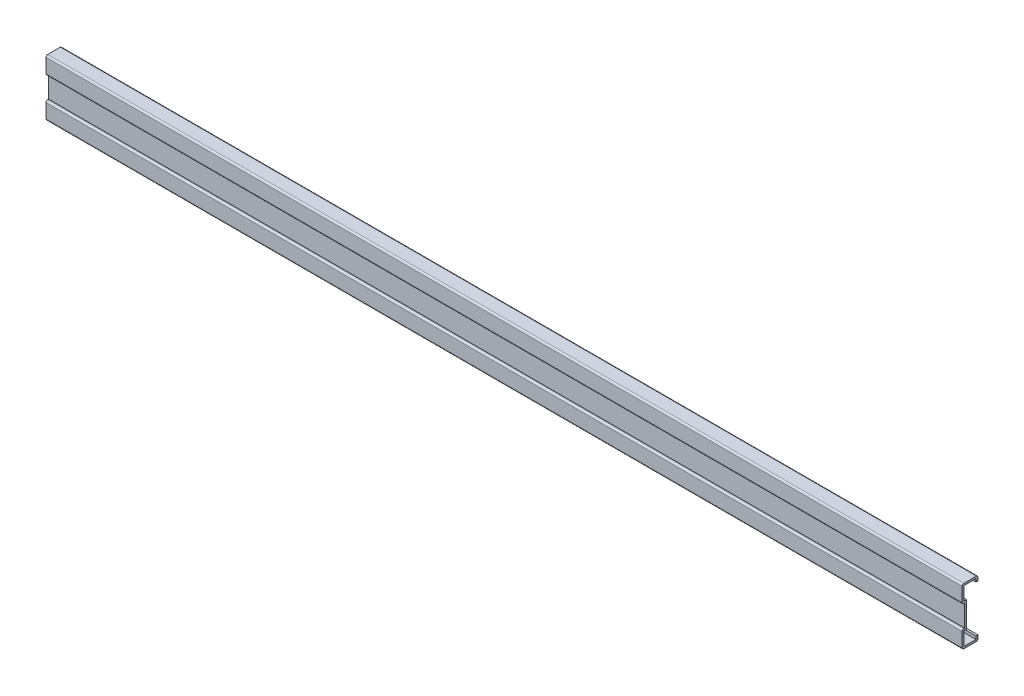
SolidWorks part; units mm, degrees
ref_plane "Спереди" through (0, 0, 0) normal (0, 0, 1) x (1, 0, 0)
ref_plane "Сверху" through (0, 0, 0) normal (0, 1, 0) x (1, 0, 0)
ref_plane "Справа" through (0, 0, 0) normal (1, 0, 0) x (0, 0, -1)
sketch "Эскиз1" plane through (0, 0, 0) normal (1, 0, 0) x (0, 0, -1)
  line L0 (0, 6.5) -> (0, -6.5)
  line L1 (-12.4481, 0) -> (26.4522, 0) construction
  line L2 (0, -6.5) -> (-0.5, -6.5)
  line L3 (-1.5, -7.5) -> (-1.5, -16)
  line L4 (-0.5, -17) -> (7, -17)
  line L5 (8, -16) -> (8, -14)
  line L6 (8, 16) -> (8, 14)
  line L7 (-0.5, 17) -> (7, 17)
  line L8 (-1.5, 7.5) -> (-1.5, 16)
  line L9 (0, 6.5) -> (-0.5, 6.5)
  arc A0 (7, -17) -> (8, -16) centre (7, -16) ccw
  arc A1 (-1.5, -7.5) -> (-0.5, -6.5) centre (-0.5, -7.5) cw
  arc A2 (-1.5, 16) -> (-0.5, 17) centre (-0.5, 16) cw
  arc A3 (-1.5, -16) -> (-0.5, -17) centre (-0.5, -16) ccw
  arc A4 (-1.5, 7.5) -> (-0.5, 6.5) centre (-0.5, 7.5) ccw
  arc A5 (7, 17) -> (8, 16) centre (7, 16) cw
  point P14 (0, 0)
  point P16 (8, -17)
  point P20 (0, 0)
  point P26 (-1.5, -17)
  point P30 (0, 0)
  dimension "D1" = 1
  dimension "D2" = 1
extrude "Вытянуть-Тонкостенный3" add sketch "Эскиз1" along normal blind 550 thin
